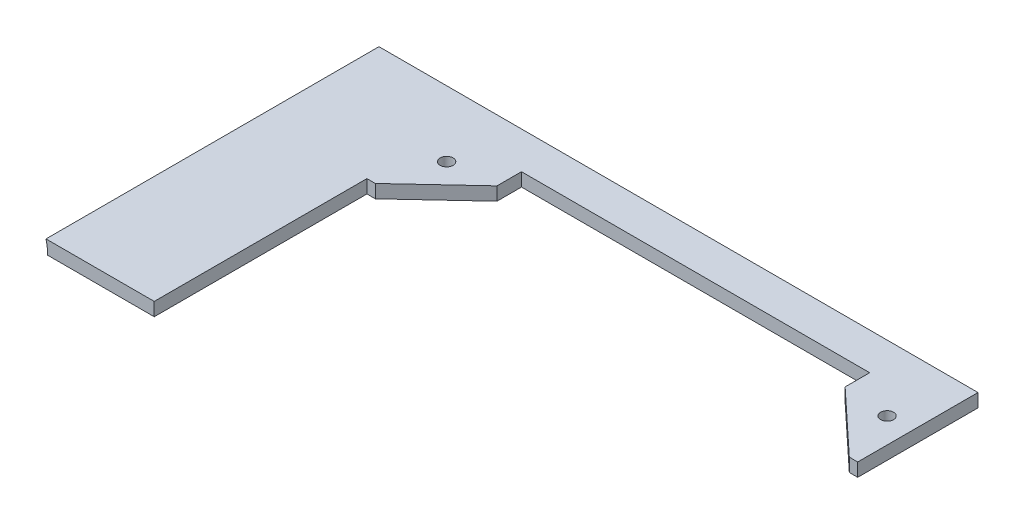
SolidWorks part; units mm, degrees
material "AISI 4130 Steel, annealed at 865C"
ref_plane "X-Y Datum" through (0, 0, 0) normal (0, 0, 1) x (1, 0, 0)
ref_plane "X-Z Datum" through (0, 0, 0) normal (0, 1, 0) x (1, 0, 0)
ref_plane "Y-Z Datum" through (0, 0, 0) normal (1, 0, 0) x (0, 0, -1)
sketch "Sketch1" plane through (0, 0, 0) normal (0, 1, 0) x (1, 0, 0)
  line L1 (-95.25, -38.1) -> (95.25, -38.1)
  line L2 (-95.25, -38.1) -> (-95.25, 38.1)
  line L3 (-95.25, 38.1) -> (95.25, 38.1)
  line L4 (95.25, -38.1) -> (95.25, 38.1)
  line L5 (-95.25, -38.1) -> (95.25, 38.1) construction
  line L6 (-95.25, 38.1) -> (95.25, -38.1) construction
  point P0 (0, 0)
  dimension "D1" = 190.5
  dimension "D2" = 76.2
extrude "Boss-Extrude1" add sketch "Sketch1" along normal blind 3.175 contours L3 L4 L1 L2
sketch "Sketch2" plane through (0, 3.175, 0) normal (0, 1, 0) x (1, 0, 0)
  line L0 (-56.5, 12.6) -> (-41.5, 26.6) construction
  line L1 (-41.5, 26.6) -> (-41.5, 32.45) construction
  line L2 (-41.5, 32.45) -> (41.5, 32.45) construction
  line L3 (41.5, 32.45) -> (41.5, 26.6) construction
  line L4 (-95.25, 38.1) -> (-95.25, -38.1)
  line L5 (-95.25, -38.1) -> (95.25, -38.1)
  line L6 (95.25, -38.1) -> (95.25, 38.1)
  line L7 (95.25, 38.1) -> (-95.25, 38.1)
  line L8 (-95.25, 38.1) -> (-95.25, -38.1)
  line L9 (-95.25, -38.1) -> (95.25, -38.1)
  line L10 (95.25, -38.1) -> (95.25, 38.1)
  line L11 (95.25, 38.1) -> (-95.25, 38.1)
  line L12 (41.5, 26.6) -> (56.5, 12.6) construction
  line L13 (-56.5, 12.6) -> (-41.5, 26.6)
  line L14 (-41.5, 26.6) -> (-41.5, 32.45)
  line L15 (-41.5, 32.45) -> (41.5, 32.45)
  line L16 (41.5, 32.45) -> (41.5, 26.6)
  line L17 (41.5, 26.6) -> (56.5, 12.6)
  line L18 (56.5, 12.6) -> (95.25, 12.6)
  line L19 (-56.5, 12.6) -> (-58.5, 12.6)
  line L20 (58.5, -451.9) -> (58.5, 38.1) construction
  line L21 (58.5, 12.6) -> (58.5, 38.1)
  line L22 (-58.5, 38.1) -> (-58.5, -451.9) construction
  line L23 (-58.5, 38.1) -> (-58.5, -38.1)
  circle A0 centre (-52.5052, 25.6052) radius 1.5453 construction
  circle A1 centre (52.5, 25.6052) radius 1.5453 construction
  circle A2 centre (-52.5052, 25.6052) radius 1.5453
  circle A3 centre (52.5, 25.6052) radius 1.5453
  line M6 (-95.25, -38.1) -> (95.25, -38.1)
  line M7 (95.25, -38.1) -> (95.25, 38.1)
  line M8 (95.25, 38.1) -> (-95.25, 38.1)
  dimension "D1" = 0
extrude "Cut-Extrude4" cut sketch "Sketch2" against normal through all contours L13 L19 L8 L18 L17 L16 L15 L14 M6 M7 | L21 L18 L10 M8 | A2 | A3
sketch "Sketch3" plane through (0, 0, -38.1) normal (0, 0, -1) x (-1, 0, 0)
  line L4 (95.25, 3.175) -> (-58.5, 3.175)
  line L5 (-58.5, 3.175) -> (-58.5, 0)
  line L6 (-58.5, 0) -> (95.25, 0)
  line L7 (95.25, 0) -> (95.25, 3.175)
  line L8 (95.25, 3.175) -> (-58.5, 3.175)
  line L9 (-58.5, 3.175) -> (-58.5, 0)
  line L10 (-58.5, 0) -> (95.25, 0)
  line L11 (95.25, 0) -> (95.25, 3.175)
  dimension "D1" = 0
extrude "Boss-Extrude2" add sketch "Sketch3" along normal blind 3.175
sketch "Sketch6" plane through (0, 0, 0) normal (0, -1, 0) x (1, 0, 0)
  line L0 (58.5, -41.275) -> (-95.25, -41.275) construction
  line L1 (58.5, -41.275) -> (-95.25, -41.275) construction
  line L14 (58.5, -38.1) -> (-95.25, -38.1) construction
  dimension "D1" = 3.175
sketch "Sketch7" plane through (0, 3.175, 0) normal (0, 1, 0) x (1, 0, 0)
  line L2 (-95.25, 38.1) -> (58.5, 38.1)
  line L3 (-95.25, 38.1) -> (58.5, 38.1) construction
  dimension "D1" = 3.175
sketch3d "3DSketch6"
  line L0 (-96.6, 0, -54.0839) -> (-96.6, 0, 450.4546)
sweep "Cut-Sweep1" cut path "3DSketch6" circular profile diameter 25.4 parameters "D3"=25.4
